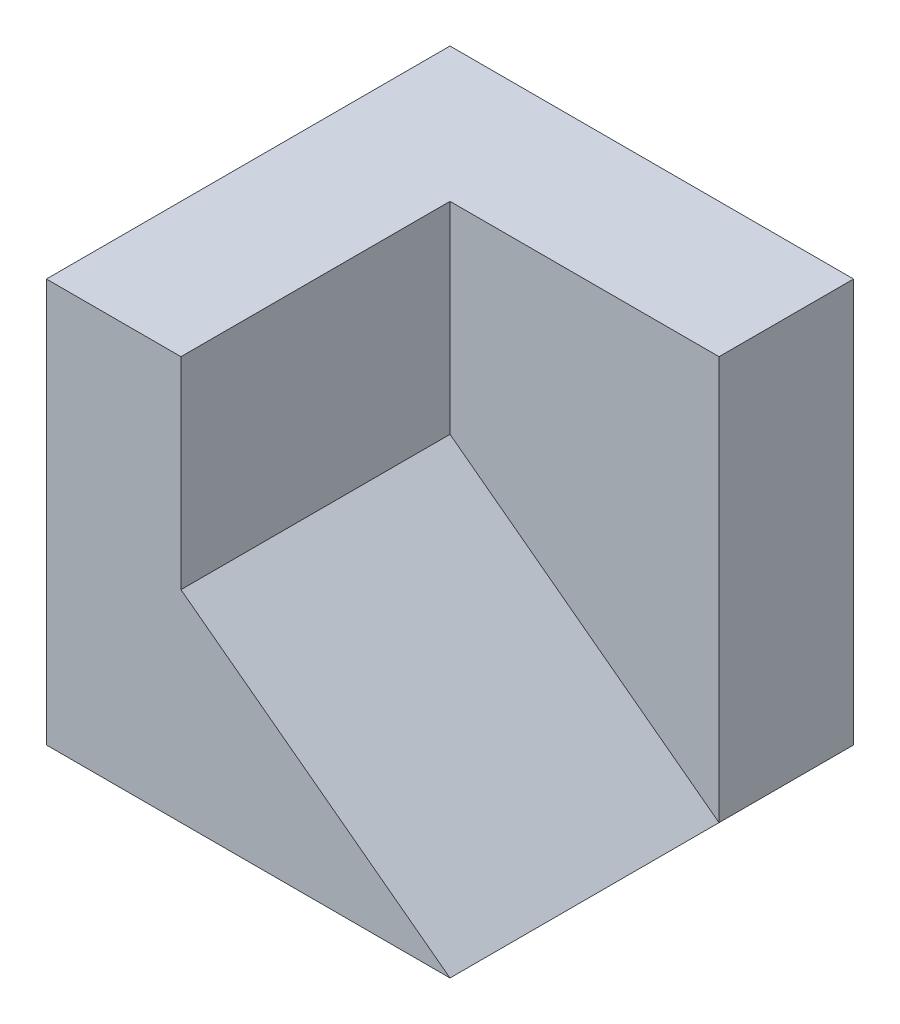
SolidWorks part; units mm, degrees
ref_plane "Alzado" through (0, 0, 0) normal (0, 0, 1) x (1, 0, 0)
ref_plane "Planta" through (0, 0, 0) normal (0, 1, 0) x (1, 0, 0)
ref_plane "Vista lateral" through (0, 0, 0) normal (1, 0, 0) x (0, 0, -1)
sketch "Croquis1" plane through (0, 0, 0) normal (0, 1, 0) x (1, 0, 0)
  line L1 (0, 0) -> (60, 0)
  line L2 (0, 0) -> (0, -60)
  line L3 (0, -60) -> (60, -60)
  line L4 (60, 0) -> (60, -60)
  dimension "D1" = 60
  dimension "D2" = 60
extrude "Saliente-Extruir1" add sketch "Croquis1" along normal blind 60
sketch "Croquis2" plane through (0, 60, 0) normal (0, 1, 0) x (1, 0, 0)
  line L2 (60, -60) -> (60, 0) construction
  line L5 (0, -60) -> (60, -60) construction
  line L9 (20, -20) -> (60, -20)
  line L10 (20, -20) -> (20, -60)
  line L11 (20, -60) -> (60, -60)
  line L12 (60, -20) -> (60, -60)
  dimension "D1" = 20
extrude "Cortar-Extruir1" cut sketch "Croquis2" against normal blind 30
sketch "Croquis3" plane through (0, 0, 60) normal (0, 0, 1) x (1, 0, 0)
  line L0 (20, 30) -> (60, 30)
  line L1 (60, 30) -> (60, 0)
  line L2 (60, 0) -> (20, 30)
extrude "Cortar-Extruir2" cut sketch "Croquis3" against normal blind 40
